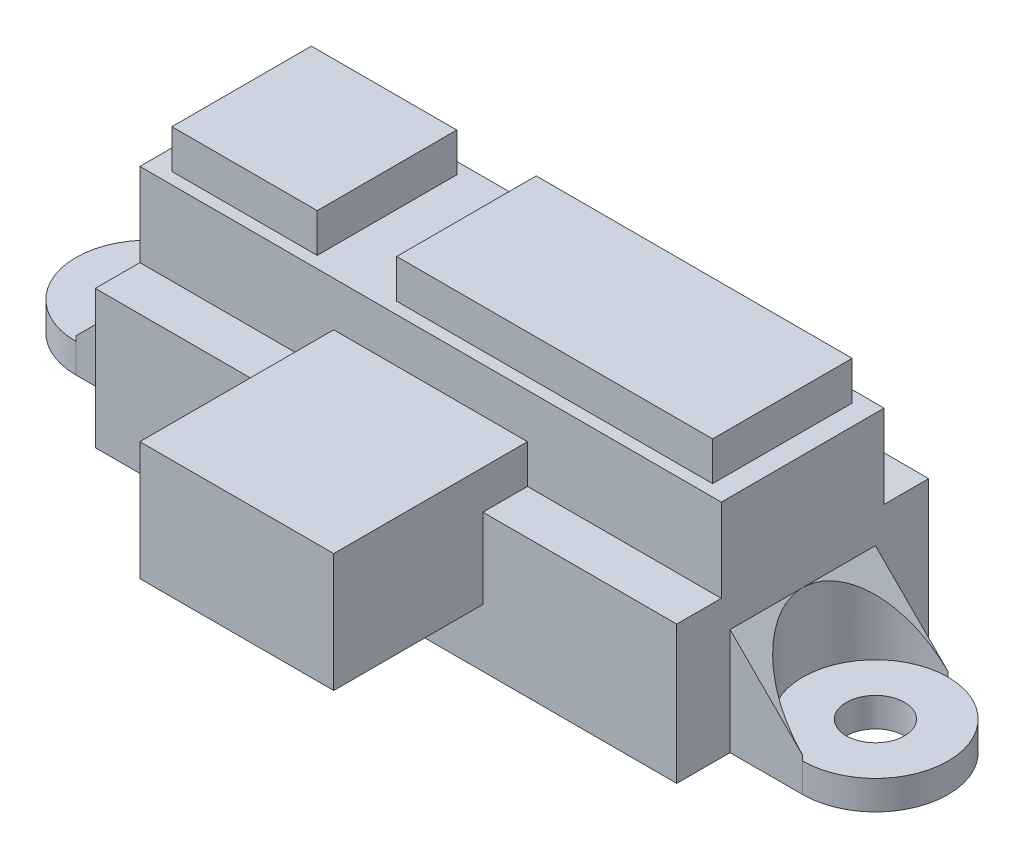
SolidWorks part; units mm, degrees
ref_plane "Front Plane" through (0, 0, 0) normal (0, 0, 1) x (1, 0, 0)
ref_plane "Top Plane" through (0, 0, 0) normal (0, 1, 0) x (1, 0, 0)
ref_plane "Right Plane" through (0, 0, 0) normal (1, 0, 0) x (0, 0, -1)
sketch "Sketch1" plane through (0, 0, 0) normal (0, 1, 0) x (1, 0, 0)
  line L1 (-15, 6.5) -> (15, 6.5)
  line L2 (-15, 6.5) -> (-15, -6.5)
  line L3 (-15, -6.5) -> (15, -6.5)
  line L4 (15, 6.5) -> (15, -6.5)
  line L5 (-15, 6.5) -> (15, -6.5) construction
  line L6 (-15, -6.5) -> (15, 6.5) construction
  point P0 (0, 0)
  dimension "D1" = 30
  dimension "D2" = 13
extrude "BottomPlateau" add sketch "Sketch1" along normal blind 7.12
sketch "Sketch3" plane through (0, 0, 0) normal (0, -1, 0) x (1, 0, 0)
  line L0 (15, 6.5) -> (15, -6.5) construction
  line L1 (-15, -6.5) -> (-15, 6.5) construction
  line L2 (-18.75, 3.75) -> (-15, 3.75)
  line L3 (-15, 3.75) -> (-15, -3.75)
  line L4 (-15, -3.75) -> (-18.75, -3.75)
  line L5 (18.75, 3.75) -> (15, 3.75)
  line L6 (18.75, -3.75) -> (15, -3.75)
  line L7 (15, -3.75) -> (15, 3.75)
  arc A0 (-18.75, 3.75) -> (-18.75, -3.75) centre (-18.75, 0) ccw
  arc A1 (18.75, -3.75) -> (18.75, 3.75) centre (18.75, 0) ccw
  arc A2 (-15, 0) -> (-18.75, 3.75) centre (-18.75, 0) ccw construction
  arc A3 (-18.75, -3.75) -> (-15, 0) centre (-18.75, 0) ccw construction
  arc A4 (18.75, 3.75) -> (15, 0) centre (18.75, 0) ccw construction
  arc A5 (15, 0) -> (18.75, -3.75) centre (18.75, 0) ccw construction
  circle A6 centre (-18.75, 0) radius 1.5
  circle A7 centre (18.75, 0) radius 1.5
  dimension "D1" = 7.5
  dimension "D2" = 3
extrude "ScrewSockets" add sketch "Sketch3" against normal blind 1.5
sketch "Sketch4" plane through (0, 7.12, 0) normal (0, 1, 0) x (1, 0, 0)
  line L0 (15, -6.5) -> (15, 6.5) construction
  line L1 (-15, -4.2) -> (15, -4.2)
  line L2 (-15, -4.2) -> (-15, 4.2)
  line L3 (-15, 4.2) -> (15, 4.2)
  line L4 (15, -4.2) -> (15, 4.2)
  line L5 (-15, -4.2) -> (15, 4.2) construction
  line L6 (-15, 4.2) -> (15, -4.2) construction
  point P0 (0, 0)
  dimension "D1" = 8.4
extrude "TopPlateau" add sketch "Sketch4" along normal blind 4.3
sketch "Sketch5" plane through (0, 11.42, 0) normal (0, 1, 0) x (1, 0, 0)
  line L0 (-13.95, 0) -> (13.95, 0) construction
  line L1 (-6.45, -3.6) -> (-13.95, -3.6)
  line L2 (-6.45, -3.6) -> (-6.45, 3.6)
  line L3 (-6.45, 3.6) -> (-13.95, 3.6)
  line L4 (-13.95, -3.6) -> (-13.95, 3.6)
  line L5 (-6.45, -3.6) -> (-13.95, 3.6) construction
  line L6 (-6.45, 3.6) -> (-13.95, -3.6) construction
  line L7 (-2.35, -3.6) -> (13.95, -3.6)
  line L8 (-2.35, -3.6) -> (-2.35, 3.6)
  line L9 (-2.35, 3.6) -> (13.95, 3.6)
  line L10 (13.95, -3.6) -> (13.95, 3.6)
  line L11 (-2.35, -3.6) -> (13.95, 3.6) construction
  line L12 (-2.35, 3.6) -> (13.95, -3.6) construction
  point P0 (-10.2, 0)
  point P5 (5.8, 0)
  point P10 (0, 0)
  dimension "D1" = 7.2
  dimension "D2" = 7.5
  dimension "D3" = 4.1
  dimension "D4" = 16.3
extrude "SensorSockets" add sketch "Sketch5" along normal blind 2
sketch "Sketch6" plane through (0, 1.5, 0) normal (0, 1, 0) x (1, 0, 0)
  line L0 (18.75, 3.75) -> (15, 3.75)
  line L1 (15, 3.75) -> (15, -3.75)
  line L2 (15, -3.75) -> (18.75, -3.75)
  line L3 (-18.75, 3.75) -> (-15, 3.75)
  line L4 (-15, 3.75) -> (-15, -3.75)
  line L5 (-15, -3.75) -> (-18.75, -3.75)
  arc A0 (-18.75, -3.75) -> (-18.75, 3.75) centre (-18.75, 0) ccw
  arc A1 (18.75, 3.75) -> (18.75, -3.75) centre (18.75, 0) ccw
  arc A2 (-18.75, 3.75) -> (-18.75, -3.75) centre (-18.75, 0) ccw construction
  arc A3 (18.75, -3.75) -> (18.75, 3.75) centre (18.75, 0) ccw construction
  line M3 (-15, 3.75) -> (-18.75, 3.75)
  line M5 (-18.75, -3.75) -> (-15, -3.75)
  line M6 (-15, -3.75) -> (-15, 3.75)
extrude "ExtrudedSlants" add sketch "Sketch6" along normal blind 4 contours A0 M5 M6 | A0 L4 M3 | A1 L0 L1 | A1 L1 L2
sketch "Sketch7" plane through (0, 0, 3.75) normal (0, 0, 1) x (1, 0, 0)
  line L0 (-15, 5.5) -> (-18.75, 1.75)
  line L1 (-18.75, 5.5) -> (-18.75, 1.5) construction
  line L2 (-18.75, 1.75) -> (-18.75, 5.5)
  line L3 (-18.75, 5.5) -> (-15, 5.5)
  line L4 (15, 5.5) -> (18.75, 1.75)
  line L5 (18.75, 5.5) -> (18.75, 1.5) construction
  line L6 (18.75, 1.75) -> (18.75, 5.5)
  line L7 (18.75, 5.5) -> (15, 5.5)
  dimension "D1" = 45
  dimension "D2" = 45
extrude "45Slants" cut sketch "Sketch7" against normal up to surface (7.5 mm away) up to face at (-17.25, 2.5, -3.75)
sketch "Connection" plane through (0, 0, 4.2) normal (0, 0, 1) x (1, 0, 0)
  line L1 (-5, 9.12) -> (5, 9.12)
  line L2 (-5, 9.12) -> (-5, 3)
  line L3 (-5, 3) -> (5, 3)
  line L4 (5, 9.12) -> (5, 3)
  line L5 (-5, 9.12) -> (5, 3) construction
  line L6 (-5, 3) -> (5, 9.12) construction
  point P0 (0, 6.06)
  dimension "D1" = 10
  dimension "D2" = 6.12
  dimension "D3" = 3
extrude "Boss-Extrude6" add sketch "Connection" along normal blind 10
